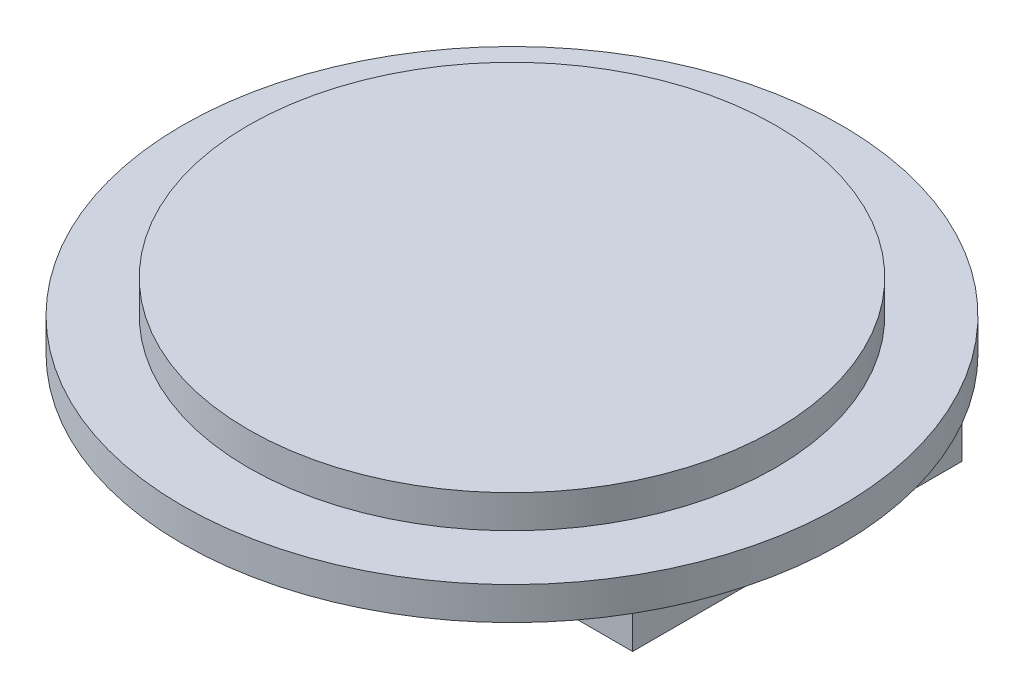
SolidWorks part; units mm, degrees
ref_plane "Plano frontal" through (0, 0, 0) normal (0, 0, 1) x (1, 0, 0)
ref_plane "Plano superior" through (0, 0, 0) normal (0, 1, 0) x (1, 0, 0)
ref_plane "Plano direito" through (0, 0, 0) normal (1, 0, 0) x (0, 0, -1)
sketch "Esboço1" plane through (0, 0, 0) normal (0, 1, 0) x (1, 0, 0)
  circle A0 centre (0, 0) radius 10
  dimension "D1" = 20
extrude "Ressalto-extrusão1" add sketch "Esboço1" along normal blind 1
sketch "Esboço2" plane through (0, 1, 0) normal (0, 1, 0) x (1, 0, 0)
  circle A0 centre (0, 0) radius 8
  dimension "D1" = 16
extrude "Ressalto-extrusão2" add sketch "Esboço2" along normal blind 1
sketch "Esboço3" plane through (0, 0, 0) normal (0, -1, 0) x (1, 0, 0)
  line L1 (-8.6603, -5) -> (8.6603, -5)
  line L2 (-8.6603, -5) -> (-8.6603, 5)
  line L3 (-8.6603, 5) -> (8.6603, 5)
  line L4 (8.6603, -5) -> (8.6603, 5)
  line L5 (-8.6603, -5) -> (8.6603, 5) construction
  line L6 (-8.6603, 5) -> (8.6603, -5) construction
  circle A0 centre (0, 0) radius 10 construction
  point P0 (0, 0)
  dimension "D1" = 10
extrude "Ressalto-extrusão3" add sketch "Esboço3" along normal blind 1
